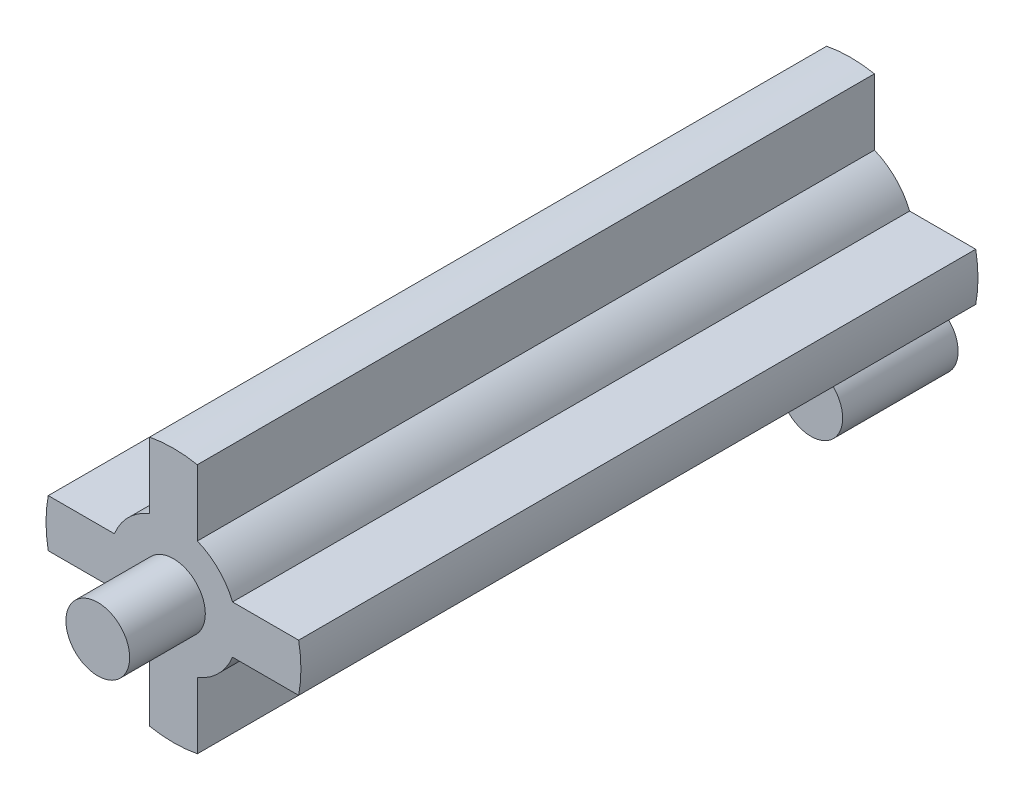
SolidWorks part; units mm, degrees
ref_plane "Front Plane" through (0, 0, 0) normal (0, 0, 1) x (1, 0, 0)
ref_plane "Top Plane" through (0, 0, 0) normal (0, 1, 0) x (1, 0, 0)
ref_plane "Right Plane" through (0, 0, 0) normal (1, 0, 0) x (0, 0, -1)
sketch "Sketch1" plane through (0, 0, 0) normal (0, 0, 1) x (1, 0, 0)
  circle A0 centre (0, 0) radius 16
  dimension "D1" = 32
extrude "Boss-Extrude1" add sketch "Sketch1" along normal blind 85
sketch "Sketch2" plane through (0, 0, 85) normal (0, 0, 1) x (1, 0, 0)
  circle A0 centre (0, 0) radius 4
  dimension "D1" = 8
sketch "Sketch3" plane through (0, 0, 0) normal (0, 0, -1) x (-1, 0, 0)
  circle A0 centre (0, 0) radius 4
  dimension "D1" = 8
extrude "Cut-Extrude2" cut sketch "Sketch3" against normal blind 5
sketch "Sketch4" plane through (0, 0, 0) normal (0, 0, -1) x (-1, 0, 0)
  line L0 (0, -16) -> (0, -8) construction
  line L1 (8, 0) -> (16, 0) construction
  line L2 (0, 7.8049) -> (0, 16) construction
  line L3 (-8, 0) -> (-16, 0) construction
  line L4 (-15.7162, 3) -> (-7.4162, 3)
  line L6 (-7.4162, -3) -> (-15.7162, -3)
  line L7 (-3, -7.4162) -> (-3, -15.7162)
  line L9 (3, -15.7162) -> (3, -7.4162)
  line L10 (7.4162, 3) -> (15.7162, 3)
  line L12 (15.7162, -3) -> (7.4162, -3)
  line L13 (3, 15.7162) -> (3, 7.4162)
  line L15 (-3, 7.4162) -> (-3, 15.7162)
  arc A0 (-3, 7.4162) -> (-7.4162, 3) centre (0, 0) ccw
  arc A1 (15.7162, -3) -> (15.7162, 3) centre (0, 0) ccw
  circle A2 centre (0, 0) radius 16 construction
  arc A3 (-7.4162, -3) -> (-3, -7.4162) centre (0, 0) ccw
  arc A4 (7.4162, 3) -> (3, 7.4162) centre (0, 0) ccw
  arc A5 (3, -7.4162) -> (7.4162, -3) centre (0, 0) ccw
  arc A6 (-3, -15.7162) -> (3, -15.7162) centre (0, 0) ccw
  arc A7 (-15.7162, 3) -> (-15.7162, -3) centre (0, 0) ccw
  arc A8 (3, 15.7162) -> (-3, 15.7162) centre (0, 0) ccw
  dimension "D8" = 8
  dimension "D1" = 3
  dimension "D2" = 3
  dimension "D3" = 3
  dimension "D4" = 3
  dimension "D5" = 3
  dimension "D6" = 3
  dimension "D7" = 3
extrude "Cut-Extrude3" cut sketch "Sketch4" against normal through all flip side to cut
sketch "Sketch5" plane through (0, 0, 0) normal (0, 0, 1) x (1, 0, 0)
  circle A1 centre (9.5329, -9.2187) radius 3.975
  dimension "7.95" = 7.95
extrude "Boss-Extrude2" add sketch "Sketch5" along normal blind 14.5 separate body
extrude "Boss-Extrude3" add sketch "Sketch2" along normal blind 9.5
